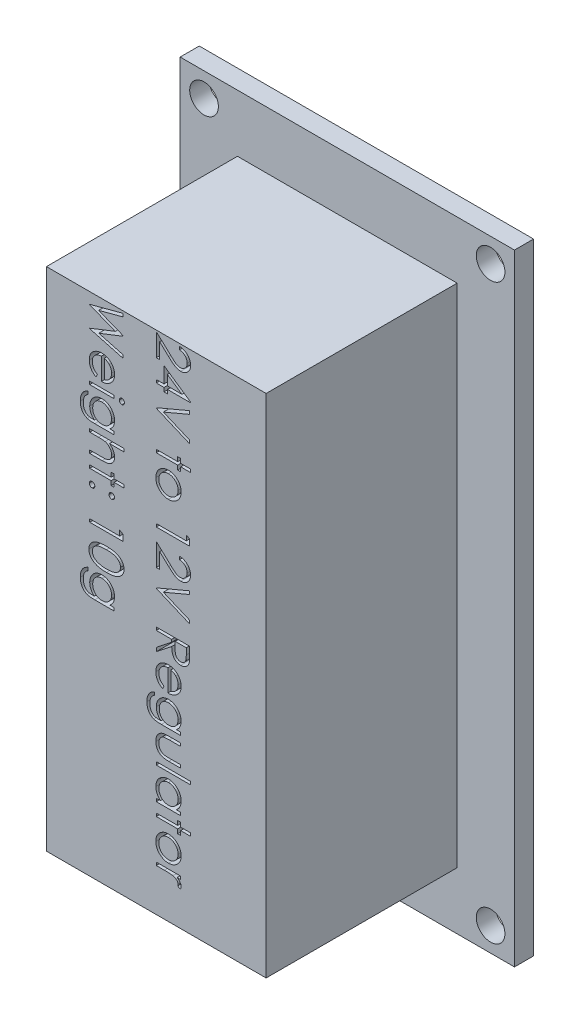
SolidWorks part; units mm, degrees
ref_plane "Front Plane" through (0, 0, 0) normal (0, 0, 1) x (1, 0, 0)
ref_plane "Top Plane" through (0, 0, 0) normal (0, 1, 0) x (1, 0, 0)
ref_plane "Right Plane" through (0, 0, 0) normal (1, 0, 0) x (0, 0, -1)
sketch "Sketch1" plane through (0, 0, 0) normal (0, 0, 1) x (1, 0, 0)
  line L0 (-17.5, 32.5) -> (17.5, 32.5)
  line L1 (-17.5, 32.5) -> (-17.5, -32.5)
  line L2 (-17.5, -32.5) -> (17.5, -32.5)
  line L3 (17.5, 32.5) -> (17.5, -32.5)
  line L4 (0, -32.5) -> (0, 32.5) construction
  line L5 (-17.5, 0) -> (17.5, 0) construction
  circle A0 centre (-15, 30) radius 1.5
  circle A1 centre (15, 30) radius 1.5
  circle A2 centre (15, -30) radius 1.5
  circle A3 centre (-15, -30) radius 1.5
  point P16 (0, 0)
  point P17 (0, 0)
  dimension "D3" = 3
  dimension "D4" = 3
  dimension "D5" = 3
  dimension "D6" = 3
  dimension "D1" = 35
  dimension "D2" = 65
  dimension "D7" = 2.5
  dimension "D8" = 2.5
  dimension "D9" = 2.5
  dimension "D10" = 2.5
  dimension "D11" = 2.5
  dimension "D12" = 2.5
  dimension "D13" = 2.5
  dimension "D14" = 2.5
extrude "Boss-Extrude1" add sketch "Sketch1" along normal blind 2
sketch "Sketch2" plane through (0, 0, 2) normal (0, 0, 1) x (1, 0, 0)
  line L0 (17.5, 32.5) -> (-17.5, 32.5) construction
  line L1 (-11.5, -26.5) -> (11.5, -26.5)
  line L2 (-11.5, -26.5) -> (-11.5, 26.5)
  line L3 (-11.5, 26.5) -> (11.5, 26.5)
  line L4 (11.5, -26.5) -> (11.5, 26.5)
  line L5 (-11.5, -26.5) -> (11.5, 26.5) construction
  line L6 (-11.5, 26.5) -> (11.5, -26.5) construction
  line L7 (17.5, -32.5) -> (17.5, 32.5) construction
  point P0 (0, 0)
  dimension "D1" = 6
  dimension "D2" = 6
extrude "Boss-Extrude2" add sketch "Sketch2" along normal blind 20
sketch "Sketch3" plane through (0, 0, 22) normal (0, 0, 1) x (1, 0, 0)
  line L0 (0, 26.5) -> (0, -26.5) construction
  line L1 (11.5, 26.5) -> (-11.5, 26.5) construction
  line L2 (-11.5, -26.5) -> (11.5, -26.5) construction
  text T0 "24V to 12V Regulator\r\nWeight: 10g"
extrude "Cut-Extrude1" cut sketch "Sketch3" against normal blind 2
